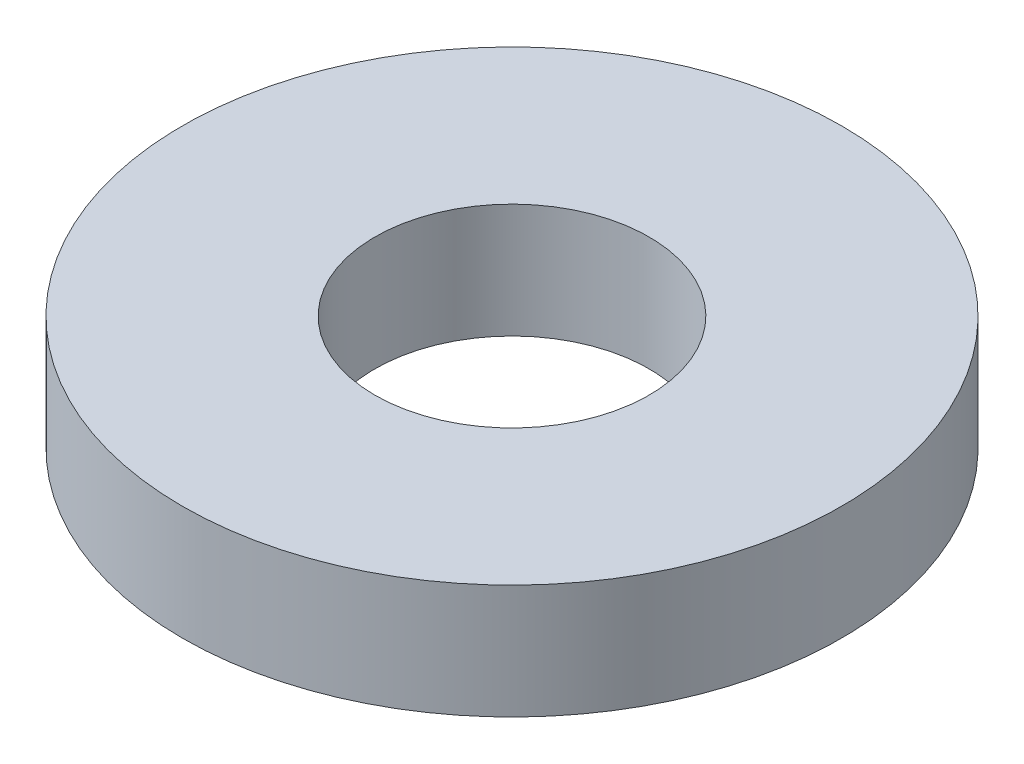
SolidWorks part; units mm, degrees
ref_plane "Front Plane" through (0, 0, 0) normal (0, 0, 1) x (1, 0, 0)
ref_plane "Top Plane" through (0, 0, 0) normal (0, 1, 0) x (1, 0, 0)
ref_plane "Right Plane" through (0, 0, 0) normal (1, 0, 0) x (0, 0, -1)
sketch "Sketch1" plane through (0, 0, 0) normal (0, 1, 0) x (1, 0, 0)
  circle A0 centre (0, 0) radius 4.7625
  dimension "OD" = 9.525
extrude "Boss-Extrude1" add sketch "Sketch1" along normal blind 1.651
sketch "Sketch5" plane through (0, 1.651, 0) normal (0, 1, 0) x (-1, 0, 0)
  circle A0 centre (0, 0) radius 1.9812
  dimension "ID" = 3.9624
extrude "Cut-Extrude1" cut sketch "Sketch5" against normal through all
